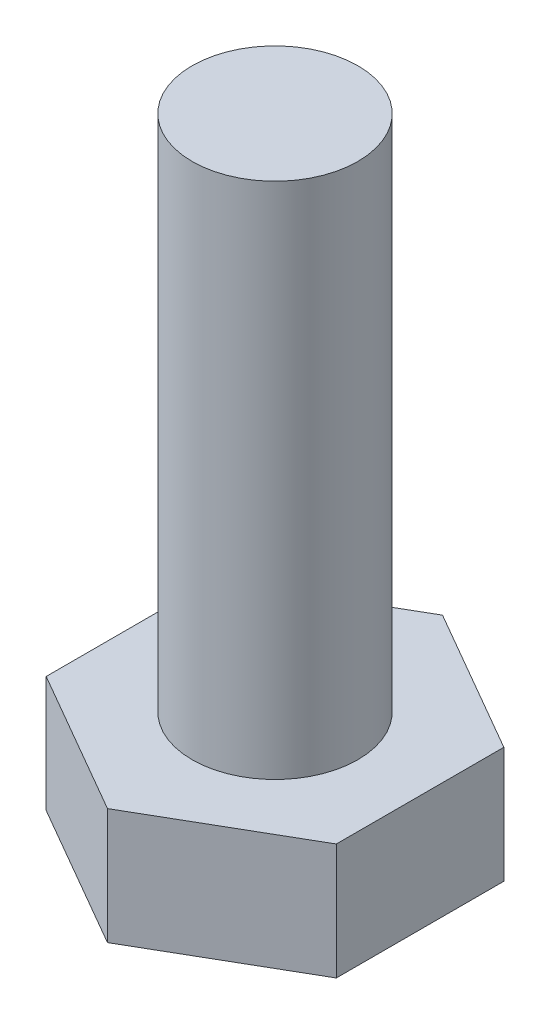
SolidWorks part; units mm, degrees
ref_plane "Front Plane" through (0, 0, 0) normal (0, 0, 1) x (1, 0, 0)
ref_plane "Top Plane" through (0, 0, 0) normal (0, 1, 0) x (1, 0, 0)
ref_plane "Right Plane" through (0, 0, 0) normal (1, 0, 0) x (0, 0, -1)
sketch "Sketch1" plane through (0, 0, 0) normal (0, 1, 0) x (1, 0, 0)
  line L1 (0, 8.0829) -> (-7, 4.0415)
  line L2 (-7, 4.0415) -> (-7, -4.0415)
  line L3 (-7, -4.0415) -> (0, -8.0829)
  line L4 (0, -8.0829) -> (7, -4.0415)
  line L5 (7, -4.0415) -> (7, 4.0415)
  line L6 (7, 4.0415) -> (0, 8.0829)
  circle A0 centre (0, 0) radius 7 construction
  dimension "D1" = 14
extrude "Boss-Extrude1" add sketch "Sketch1" along normal blind 5.6
sketch "Sketch2" plane through (0, 5.6, 0) normal (0, 1, 0) x (1, 0, 0)
  circle A0 centre (0, 0) radius 4
  dimension "D1" = 8
extrude "Boss-Extrude2" add sketch "Sketch2" along normal blind 25
